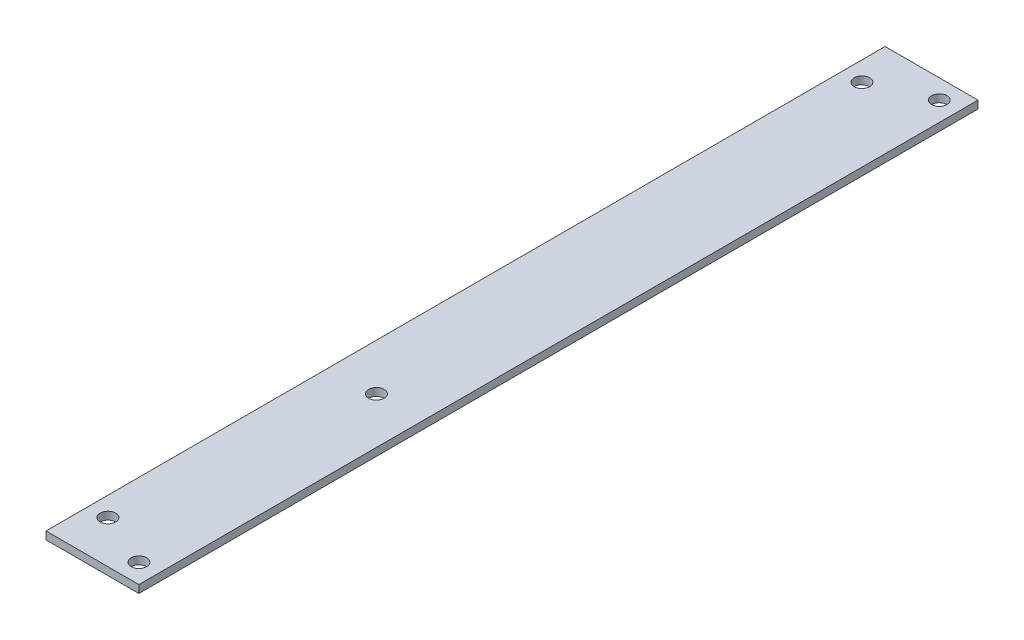
SolidWorks part; units mm, degrees
ref_plane "Front Plane" through (0, 0, 0) normal (0, 0, 1) x (1, 0, 0)
ref_plane "Top Plane" through (0, 0, 0) normal (0, 1, 0) x (1, 0, 0)
ref_plane "Right Plane" through (0, 0, 0) normal (1, 0, 0) x (0, 0, -1)
sketch "Sketch1" plane through (0, 0, 0) normal (0, 0, 1) x (1, 0, 0)
  line L0 (0, 0) -> (0, 3.175)
  line L1 (0, 3.175) -> (38.1, 3.175)
  line L2 (38.1, 3.175) -> (38.1, 0)
  line L3 (38.1, 0) -> (0, 0)
  dimension "D1" = 38.1
  dimension "D2" = 3.175
extrude "Boss-Extrude1" add sketch "Sketch1" along normal blind 344.17
sketch "Sketch3" plane through (0, 3.175, 0) normal (0, 1, 0) x (1, 0, 0)
  line L1 (0, -344.17) -> (0, 0) construction
  line L2 (19.05, -227.7075) -> (0, -227.7075) construction
  line L3 (19.05, -227.7075) -> (38.1, -227.7075) construction
  line L4 (38.1, -344.17) -> (38.1, 0) construction
  line L5 (38.1, -344.17) -> (0, -344.17) construction
  circle A0 centre (19.05, -227.7075) radius 3.175
  point P6 (19.05, -344.17)
  dimension "D1" = 6.35
  dimension "D2" = 116.4625
extrude "Cut-Extrude1" cut sketch "Sketch3" against normal through all
sketch "Sketch4" plane through (0, 0, 0) normal (0, -1, 0) x (1, 0, 0)
  circle A8 centre (30.1625, 336.2325) radius 3.175 construction
  circle A9 centre (7.9375, 326.7075) radius 3.175 construction
  circle A10 centre (7.9375, 17.4625) radius 3.175 construction
  circle A11 centre (30.1625, 7.9375) radius 3.175 construction
  circle A12 centre (30.1625, 336.2325) radius 3.175
  circle A13 centre (7.9375, 326.7075) radius 3.175
  circle A14 centre (7.9375, 17.4625) radius 3.175
  circle A15 centre (30.1625, 7.9375) radius 3.175
extrude "Cut-Extrude2" cut sketch "Sketch4" against normal through all and the other way through all
